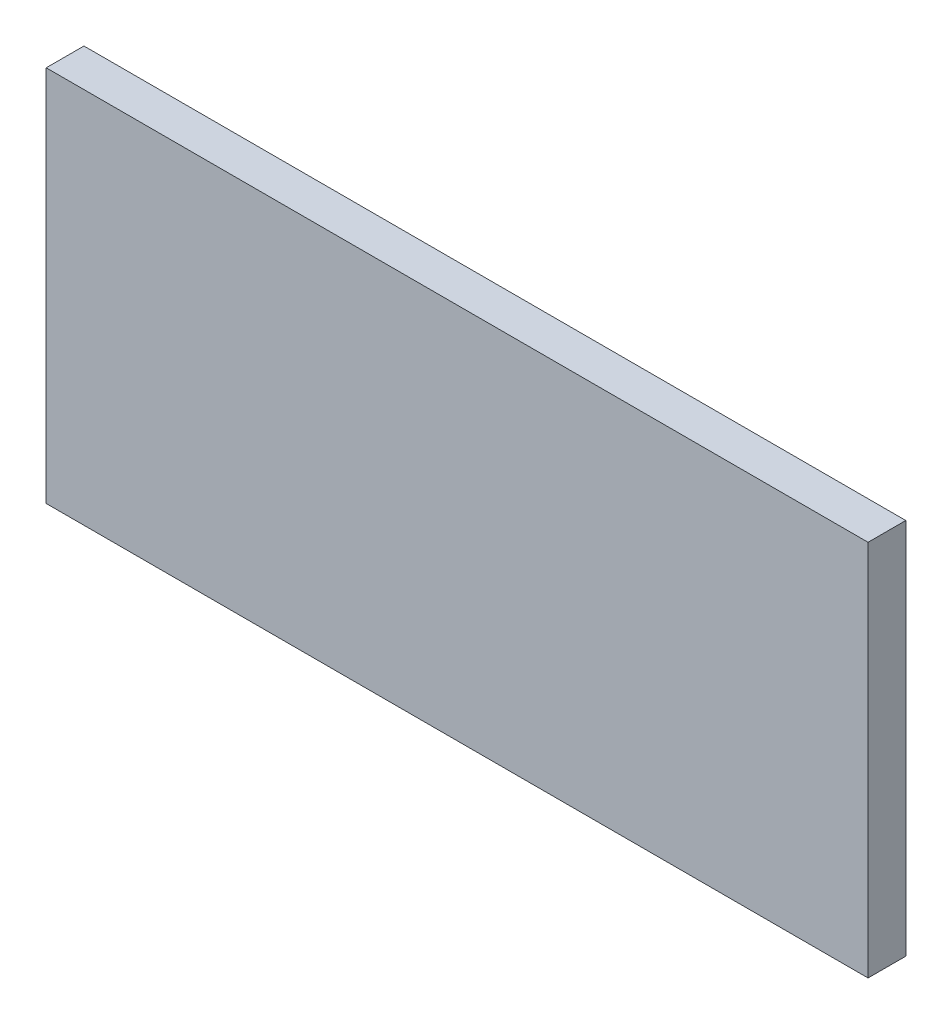
SolidWorks part; units mm, degrees
ref_plane "Front Plane" through (0, 0, 0) normal (0, 0, 1) x (1, 0, 0)
ref_plane "Top Plane" through (0, 0, 0) normal (0, 1, 0) x (1, 0, 0)
ref_plane "Right Plane" through (0, 0, 0) normal (1, 0, 0) x (0, 0, -1)
sketch "Sketch1" plane through (0, 0, 0) normal (0, 0, 1) x (1, 0, 0)
  line L0 (-177.5, -81.5) -> (-177.5, 81.5)
  line L1 (-177.5, -81.5) -> (177.5, -81.5)
  line L2 (-177.5, 81.5) -> (177.5, 81.5)
  line L3 (177.5, -81.5) -> (177.5, 81.5)
  line L4 (-177.5, -81.5) -> (177.5, 81.5) construction
  line L5 (-177.5, 81.5) -> (177.5, -81.5) construction
  point P1 (0, 0)
  dimension "D1" = 163
  dimension "D2" = 355
extrude "Boss-Extrude1" add sketch "Sketch1" along normal blind 16.3
